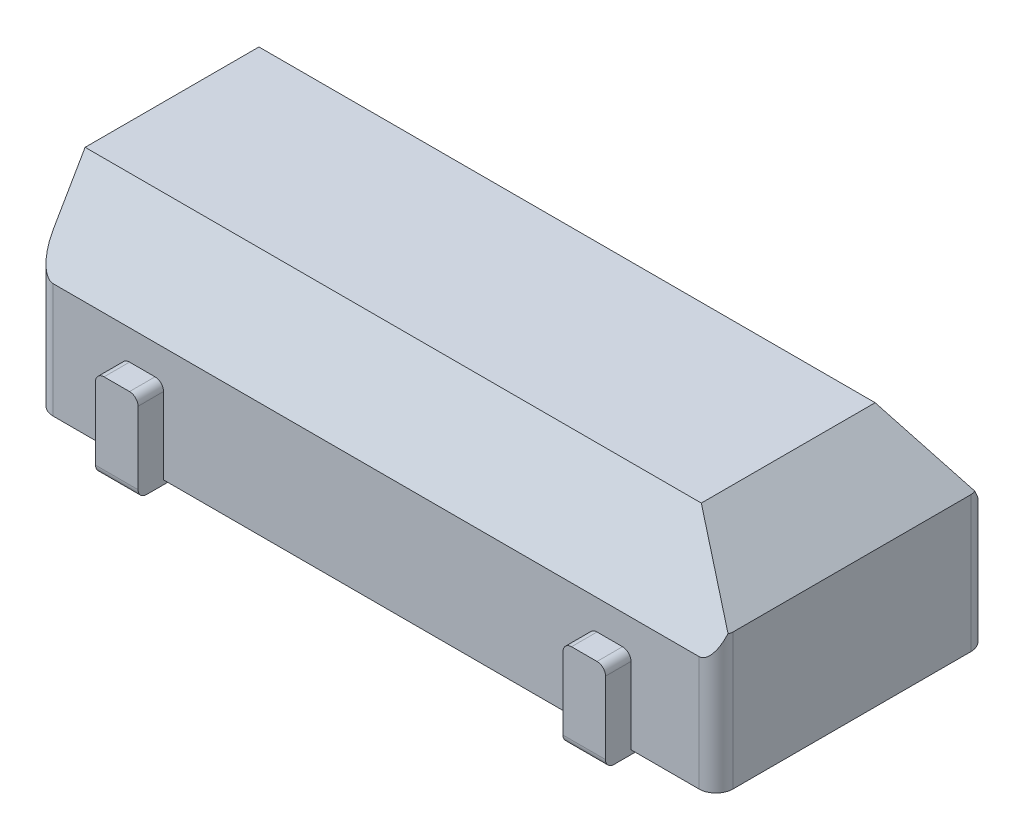
SolidWorks part; units mm, degrees
ref_plane "Спереди" through (0, 0, 0) normal (0, 0, 1) x (1, 0, 0)
ref_plane "Сверху" through (0, 0, 0) normal (0, 1, 0) x (1, 0, 0)
ref_plane "Справа" through (0, 0, 0) normal (1, 0, 0) x (0, 0, -1)
sketch "Эскиз1" plane through (0, 0, 0) normal (0, 1, 0) x (1, 0, 0)
  line L1 (-4, 1.6) -> (4, 1.6)
  line L2 (-4, 1.6) -> (-4, -1.6)
  line L3 (-4, -1.6) -> (4, -1.6)
  line L4 (4, 1.6) -> (4, -1.6)
  line L5 (-4, 1.6) -> (4, -1.6) construction
  line L6 (-4, -1.6) -> (4, 1.6) construction
  point P0 (0, 0)
  dimension "D1" = 8
  dimension "D2" = 3.2
extrude "Бобышка-Вытянуть1" add sketch "Эскиз1" along normal blind 2.35
sketch "Эскиз2" plane through (0, 0, 0) normal (0, -1, 0) x (1, 0, 0)
  line L0 (0, 2.4701) -> (0, 0) construction
  line L1 (-3, 1.9) -> (-2.5, 1.9)
  line L2 (-3, 1.9) -> (-3, 1.3)
  line L3 (-3, 1.3) -> (-2.5, 1.3)
  line L4 (-2.5, 1.9) -> (-2.5, 1.3)
  line L5 (-3, 1.9) -> (-2.5, 1.3) construction
  line L6 (-3, 1.3) -> (-2.5, 1.9) construction
  line L7 (0, 0) -> (-1.8835, 0) construction
  line L8 (3, 1.3) -> (2.5, 1.9) construction
  line L9 (3, 1.9) -> (2.5, 1.3) construction
  line L10 (2.5, 1.9) -> (2.5, 1.3)
  line L11 (3, 1.3) -> (2.5, 1.3)
  line L12 (3, 1.9) -> (3, 1.3)
  line L13 (3, 1.9) -> (2.5, 1.9)
  line L14 (3, -1.9) -> (2.5, -1.3) construction
  line L15 (3, -1.3) -> (2.5, -1.9) construction
  line L16 (-3, -1.3) -> (-2.5, -1.9) construction
  line L17 (-3, -1.9) -> (-2.5, -1.3) construction
  line L18 (3, -1.9) -> (2.5, -1.9)
  line L19 (3, -1.9) -> (3, -1.3)
  line L20 (3, -1.3) -> (2.5, -1.3)
  line L21 (2.5, -1.9) -> (2.5, -1.3)
  line L22 (-2.5, -1.9) -> (-2.5, -1.3)
  line L23 (-3, -1.3) -> (-2.5, -1.3)
  line L24 (-3, -1.9) -> (-3, -1.3)
  line L25 (-3, -1.9) -> (-2.5, -1.9)
  point P0 (-2.75, 1.6)
  point P9 (0, 2.4701)
  point P14 (2.75, 1.6)
  point P23 (2.75, -1.6)
  point P24 (-2.75, -1.6)
  dimension "D1" = 5.5
  dimension "D2" = 0.6
  dimension "D3" = 0.5
  dimension "D4" = 3.8
extrude "Бобышка-Вытянуть2" add sketch "Эскиз2" along normal blind 0.05 and the other way blind 1
fillet "Скругление1" radius 0.1 12 edges at (-2.75, -0.05, 1.9) (2.75, -0.05, 1.9) (2.75, -0.05, -1.9) (-2.75, -0.05, -1.9) (-3, 1, -1.75) (-2.5, 1, -1.75) (2.5, 1, -1.75) (3, 1, -1.75) (2.5, 1, 1.75) (3, 1, 1.75) (-3, 1, 1.75) (-2.5, 1, 1.75)
chamfer "Фаска1" distance 1 angle 30 2 edges at (0, 2.35, 1.6) (0, 2.35, -1.6)
chamfer "Фаска2" distance 0.75 angle 45 1 edges at (4, 2.35, 0)
fillet "Скругление2" radius 0.2 4 edges at (-4, 0.675, 1.6) (-4, 0.675, -1.6) (4, 0.675, 1.6) (4, 0.675, -1.6)
